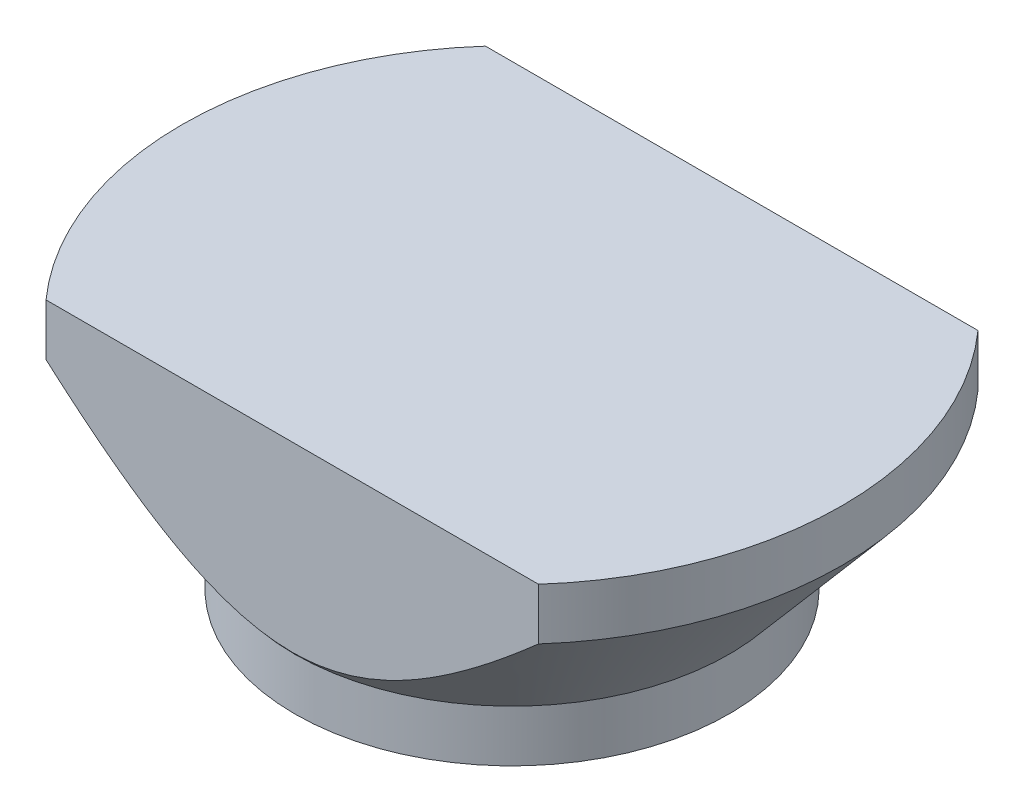
SolidWorks part; units mm, degrees
ref_plane "Front Plane" through (0, 0, 0) normal (0, 0, 1) x (1, 0, 0)
ref_plane "Top Plane" through (0, 0, 0) normal (0, 1, 0) x (1, 0, 0)
ref_plane "Right Plane" through (0, 0, 0) normal (1, 0, 0) x (0, 0, -1)
sketch "Sketch1" plane through (0, 0, 0) normal (0, 0, 1) x (1, 0, 0)
  line L0 (0, 0) -> (-21, 0)
  line L1 (-21, 0) -> (-21, 5)
  line L2 (-21, 5) -> (-31.9152, 17.9)
  line L3 (-31.9152, 17.9) -> (-31.9152, 22.9)
  line L4 (-31.9152, 22.9) -> (0, 22.9)
  line L5 (0, 22.9) -> (0, 0)
  point P3 (-31.9152, 24.2763)
  dimension "D1" = 5
  dimension "D2" = 21
  dimension "D3" = 31.9152
  dimension "D4" = 5
  dimension "D5" = 22.9
revolve "Revolve1" add sketch "Sketch1" angle 360 about L5
sketch "Sketch2" plane through (0, 0, 0) normal (0, 1, 0) x (1, 0, 0)
  line L1 (-23.8121, 31.9152) -> (23.8121, 31.9152)
  line L2 (-23.8121, 31.9152) -> (-23.8121, 21.25)
  line L3 (-23.8121, 21.25) -> (23.8121, 21.25)
  line L4 (23.8121, 31.9152) -> (23.8121, 21.25)
  line L5 (-23.8121, -21.25) -> (23.8121, -21.25)
  line L6 (-23.8121, -21.25) -> (-23.8121, -31.9152)
  line L7 (-23.8121, -31.9152) -> (23.8121, -31.9152)
  line L8 (23.8121, -21.25) -> (23.8121, -31.9152)
  circle A0 centre (0, 0) radius 31.9152 construction
  point P10 (-27.9, -15.4973)
  point P11 (27.5679, -16.0808)
  point P12 (-27.6786, 15.8894)
  point P13 (-23.5472, 21.5432)
  dimension "D1" = 47.6243
extrude "Cut-Extrude2" cut sketch "Sketch2" along normal through all
